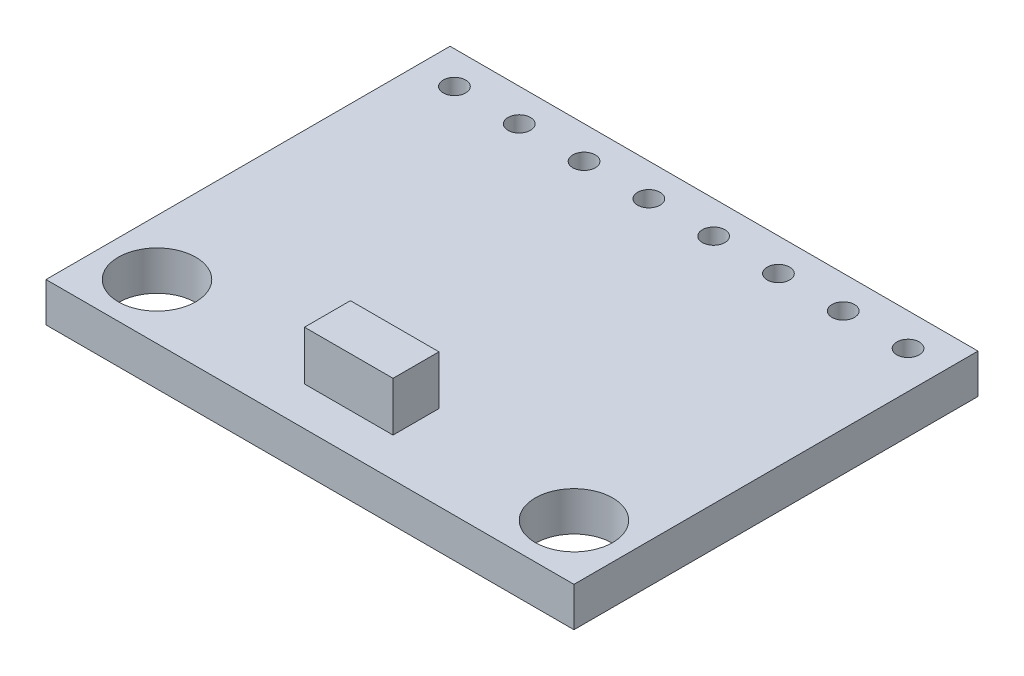
SolidWorks part; units mm, degrees
ref_plane "Front Plane" through (0, 0, 0) normal (0, 0, 1) x (1, 0, 0)
ref_plane "Top Plane" through (0, 0, 0) normal (0, 1, 0) x (1, 0, 0)
ref_plane "Right Plane" through (0, 0, 0) normal (1, 0, 0) x (0, 0, -1)
sketch "Sketch1" plane through (0, 0, 0) normal (0, 1, 0) x (1, 0, 0)
  line L0 (0, 14.385) -> (20.45, 14.385) construction
  line L1 (0, 0) -> (20.45, 0)
  line L2 (0, 0) -> (0, 15.65)
  line L3 (0, 15.65) -> (20.45, 15.65)
  line L4 (20.45, 0) -> (20.45, 15.65)
  line L13 (8.53, 13.95) -> (9.4, 13.95) construction
  line L14 (1, 13.95) -> (1.87, 13.95) construction
  line L15 (1, 13.95) -> (1, 14.82) construction
  line L16 (1, 14.82) -> (1.87, 14.82) construction
  line L17 (1.87, 13.95) -> (1.87, 14.82) construction
  line L46 (8.53, 13.95) -> (8.53, 14.82) construction
  line L47 (8.53, 14.82) -> (9.4, 14.82) construction
  line L48 (9.4, 13.95) -> (9.4, 14.82) construction
  line L49 (6.02, 13.95) -> (6.89, 13.95) construction
  line L50 (6.02, 13.95) -> (6.02, 14.82) construction
  line L51 (6.02, 14.82) -> (6.89, 14.82) construction
  line L52 (6.89, 13.95) -> (6.89, 14.82) construction
  line L53 (13.55, 13.95) -> (14.42, 13.95) construction
  line L54 (13.55, 13.95) -> (13.55, 14.82) construction
  line L55 (13.55, 14.82) -> (14.42, 14.82) construction
  line L56 (14.42, 13.95) -> (14.42, 14.82) construction
  line L57 (11.04, 13.95) -> (11.91, 13.95) construction
  line L58 (11.04, 13.95) -> (11.04, 14.82) construction
  line L59 (11.04, 14.82) -> (11.91, 14.82) construction
  line L60 (11.91, 13.95) -> (11.91, 14.82) construction
  line L61 (3.51, 13.95) -> (4.38, 13.95) construction
  line L62 (3.51, 13.95) -> (3.51, 14.82) construction
  line L63 (3.51, 14.82) -> (4.38, 14.82) construction
  line L64 (4.38, 13.95) -> (4.38, 14.82) construction
  line L65 (16.06, 13.95) -> (16.93, 13.95) construction
  line L66 (16.06, 13.95) -> (16.06, 14.82) construction
  line L67 (16.06, 14.82) -> (16.93, 14.82) construction
  line L68 (16.93, 13.95) -> (16.93, 14.82) construction
  line L69 (18.57, 13.95) -> (19.44, 13.95) construction
  line L70 (18.57, 13.95) -> (18.57, 14.82) construction
  line L71 (18.57, 14.82) -> (19.44, 14.82) construction
  line L72 (19.44, 13.95) -> (19.44, 14.82) construction
  line L73 (0.65, 3.65) -> (3.65, 0.65) construction
  line L74 (0.65, 3.65) -> (3.65, 3.65) construction
  line L75 (0.65, 3.65) -> (0.65, 0.65) construction
  line L76 (0.65, 0.65) -> (3.65, 0.65) construction
  line L77 (3.65, 3.65) -> (3.65, 0.65) construction
  line L78 (16.8, 3.65) -> (19.8, 3.65) construction
  line L79 (16.8, 3.65) -> (16.8, 0.65) construction
  line L80 (16.8, 0.65) -> (19.8, 0.65) construction
  line L81 (19.8, 3.65) -> (19.8, 0.65) construction
  line L82 (16.8, 3.65) -> (19.8, 0.65) construction
  circle A0 centre (2.15, 2.15) radius 1.5
  circle A1 centre (18.3, 2.15) radius 1.5
  circle A3 centre (1.435, 14.385) radius 0.435
  circle A14 centre (8.965, 14.385) radius 0.435
  circle A15 centre (6.455, 14.385) radius 0.435
  circle A16 centre (13.985, 14.385) radius 0.435
  circle A17 centre (11.475, 14.385) radius 0.435
  circle A18 centre (3.945, 14.385) radius 0.435
  circle A19 centre (16.495, 14.385) radius 0.435
  circle A20 centre (19.005, 14.385) radius 0.435
  dimension "D3" = 0.87
  dimension "D7" = 0.87
  dimension "D8" = 0.87
  dimension "D9" = 0.87
  dimension "D2" = 0.87
  dimension "D4" = 0.87
  dimension "D5" = 0.87
  dimension "D6" = 0.87
  dimension "D16" = 0.87
  dimension "D19" = 0.87
  dimension "D22" = 0.87
  dimension "D25" = 0.87
  dimension "D10" = 15.65
  dimension "D11" = 20.45
  dimension "D12" = 0.87
  dimension "D13" = 0.87
  dimension "D14" = 0.87
  dimension "D15" = 0.87
  dimension "D17" = 0.87
  dimension "D18" = 0.87
  dimension "D20" = 0.87
  dimension "D21" = 0.87
  dimension "D23" = 0.87
  dimension "D24" = 0.87
  dimension "D26" = 0.87
  dimension "D27" = 0.87
  dimension "D28" = 1.64
  dimension "D29" = 1.64
  dimension "D30" = 1.64
  dimension "D31" = 1.64
  dimension "D32" = 1.64
  dimension "D33" = 1.64
  dimension "D34" = 1.64
  dimension "D35" = 1.01
  dimension "D36" = 3
  dimension "D37" = 3
  dimension "D38" = 3
  dimension "D39" = 3
  dimension "D40" = 0.65
  dimension "D41" = 0.65
  dimension "D42" = 0.65
  dimension "D43" = 0.65
  dimension "D44" = 0.83
extrude "Boss-Extrude1" add sketch "Sketch1" along normal blind 1.524
sketch "Sketch2" plane through (0, 1.524, 0) normal (0, 1, 0) x (1, 0, 0)
  line L0 (10.225, 15.65) -> (10.225, 0) construction
  line L1 (8.5105, 3.2804) -> (11.9395, 3.2804)
  line L2 (8.5105, 3.2804) -> (8.5105, 1.5024)
  line L3 (8.5105, 1.5024) -> (11.9395, 1.5024)
  line L4 (11.9395, 3.2804) -> (11.9395, 1.5024)
  line L5 (20.45, 15.65) -> (0, 15.65) construction
  line L6 (0, 0) -> (20.45, 0) construction
  point P10 (10.225, 3.2804)
  dimension "D1" = 3.429
  dimension "D2" = 1.778
extrude "Boss-Extrude2" add sketch "Sketch2" along normal blind 1.905
